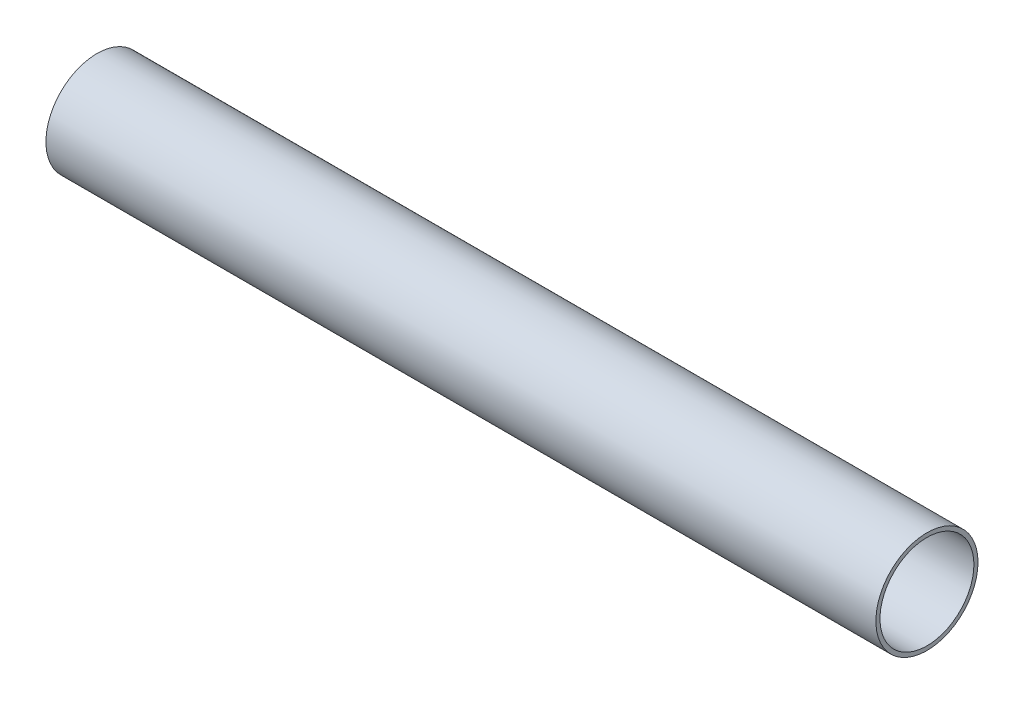
SolidWorks part; units mm, degrees
material "Thornel Mat VMA"
ref_plane "Front Plane" through (0, 0, 0) normal (0, 0, 1) x (1, 0, 0)
ref_plane "Top Plane" through (0, 0, 0) normal (0, 1, 0) x (1, 0, 0)
ref_plane "Right Plane" through (0, 0, 0) normal (1, 0, 0) x (0, 0, -1)
sketch "Sketch1" plane through (0, 0, 0) normal (1, 0, 0) x (0, 0, -1)
  circle A0 centre (0, 0) radius 12.5
  circle A1 centre (0, 0) radius 11.5
  dimension "D1" = 25
  dimension "D2" = 1
extrude "Boss-Extrude1" add sketch "Sketch1" along normal blind 203.2
